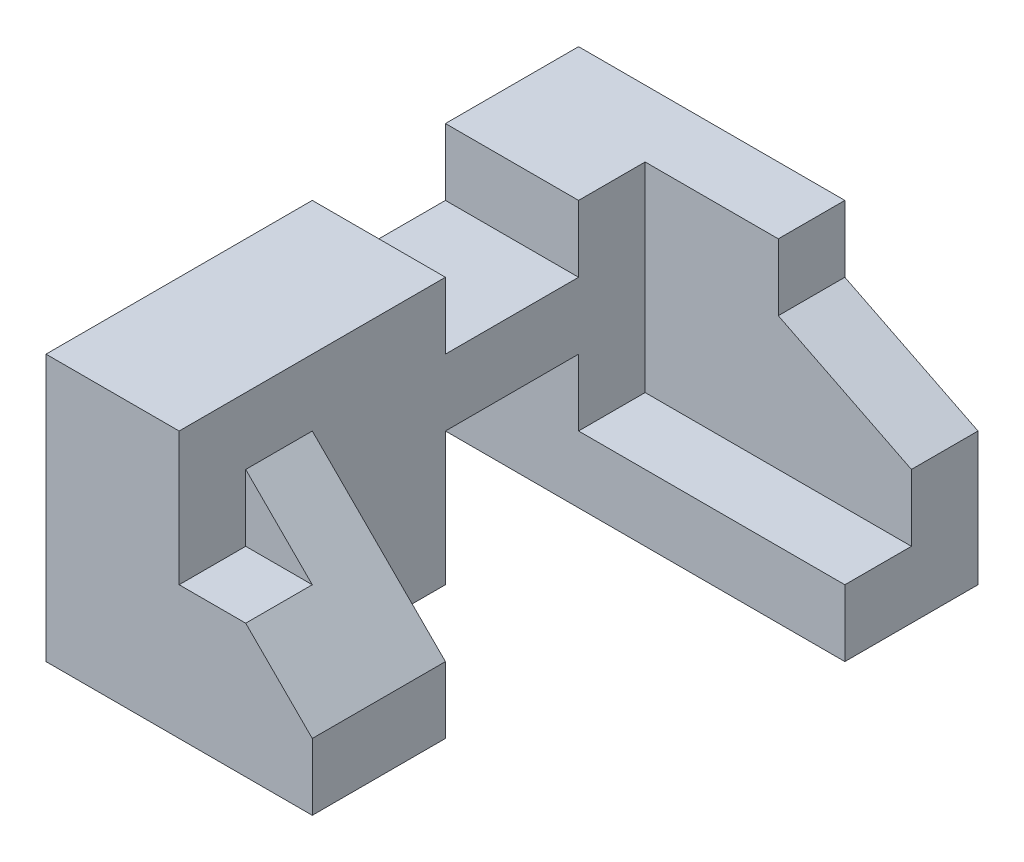
SolidWorks part; units mm, degrees
ref_plane "Front Plane" through (0, 0, 0) normal (0, 0, 1) x (1, 0, 0)
ref_plane "Top Plane" through (0, 0, 0) normal (0, 1, 0) x (1, 0, 0)
ref_plane "Right Plane" through (0, 0, 0) normal (1, 0, 0) x (0, 0, -1)
sketch "Sketch1" plane through (0, 0, 0) normal (0, 0, 1) x (1, 0, 0)
  line L1 (3, -2) -> (-3, -2)
  line L2 (3, -2) -> (3, 2)
  line L3 (3, 2) -> (-3, 2)
  line L4 (-3, -2) -> (-3, 2)
  line L5 (3, -2) -> (-3, 2) construction
  line L6 (3, 2) -> (-3, -2) construction
  point P0 (0, 0)
  dimension "D1" = 6
  dimension "D2" = 4
extrude "Boss-Extrude1" add sketch "Sketch1" along normal blind 8
sketch "Sketch2" plane through (0, 2, 0) normal (0, 1, 0) x (1, 0, 0)
  line L0 (-3, -2) -> (-1, -2)
  line L1 (-3, -8) -> (-3, 0) construction
  line L2 (-1, -2) -> (-1, -4)
  line L3 (-1, -4) -> (-3, -4)
  line L4 (-3, -4) -> (-3, -2)
  dimension "D1" = 2
  dimension "D2" = 2
  dimension "D3" = 2
extrude "Cut-Extrude1" cut sketch "Sketch2" against normal blind 1
sketch "Sketch4" plane through (3, 0, 0) normal (1, 0, 0) x (0, 0, -1)
  line L0 (-1, 2) -> (-1, -1)
  line L1 (-8, 2) -> (0, 2) construction
  line L2 (-8, -2) -> (0, -2) construction
  line L3 (-1, -1) -> (-6, -1)
  line L4 (-6, -1) -> (-6, 2)
  line L5 (-6, 2) -> (-1, 2)
  dimension "D1" = 1
  dimension "D2" = 5
  dimension "D3" = 1
extrude "Cut-Extrude13" cut sketch "Sketch4" against normal blind 4
sketch "Sketch5" plane through (3, 0, 0) normal (1, 0, 0) x (0, 0, -1)
  line L0 (-2, -1) -> (-2, -2)
  line L1 (-6, -1) -> (-1, -1) construction
  line L2 (-8, -2) -> (0, -2) construction
  line L3 (-2, -2) -> (-6, -2)
  line L4 (-6, -2) -> (-6, -1)
  line L5 (-6, -1) -> (-2, -1)
  dimension "D1" = 1
extrude "Cut-Extrude14" cut sketch "Sketch5" against normal blind 4
sketch "Sketch6" plane through (-1, 0, 0) normal (1, 0, 0) x (0, 0, -1)
  line L0 (-2, -2) -> (-2, 0)
  line L1 (-2, 0) -> (-4, 0)
  line L2 (-4, 0) -> (-4, -2)
  line L3 (-6, -2) -> (-2, -2) construction
  line L4 (-4, -2) -> (-2, -2)
  dimension "D1" = 2
extrude "Cut-Extrude15" cut sketch "Sketch6" against normal through all
sketch "Sketch7" plane through (0, 0, 0) normal (0, 0, -1) x (-1, 0, 0)
  line L0 (-1, 2) -> (-1, 1)
  line L1 (-3, 2) -> (3, 2) construction
  line L2 (-1, 1) -> (-3, 0)
  line L3 (-3, -2) -> (-3, 2) construction
  line L4 (-3, 0) -> (-3, 2)
  line L5 (-3, 2) -> (-1, 2)
  dimension "D1" = 1
  dimension "D2" = 2
  dimension "D3" = 2
extrude "Cut-Extrude16" cut sketch "Sketch7" against normal blind 1
sketch "Sketch8" plane through (0, 2, 0) normal (0, 1, 0) x (1, 0, 0)
  line L0 (-1, -8) -> (-1, -7)
  line L1 (3, -8) -> (-3, -8) construction
  line L2 (-1, -7) -> (0, -7)
  line L3 (0, -7) -> (0, -8)
  line L4 (0, -8) -> (-1, -8)
  dimension "D1" = 2
  dimension "D2" = 1
extrude "Cut-Extrude17" cut sketch "Sketch8" against normal blind 2
sketch "Sketch10" plane through (0, 2, 0) normal (0, 1, 0) x (1, 0, 0)
  line L0 (3, -6) -> (1, -6)
  line L1 (-1, -6) -> (3, -6) construction
  line L2 (1, -6) -> (1, -8)
  line L3 (3, -8) -> (0, -8) construction
  line L4 (1, -8) -> (3, -8)
  line L5 (3, -8) -> (3, -6)
  dimension "D1" = 4
extrude "Cut-Extrude18" cut sketch "Sketch10" against normal through all
sketch "Sketch12" plane through (1, 0, 0) normal (1, 0, 0) x (0, 0, -1)
  line L0 (-6, 2) -> (-6, 1)
  line L1 (-6, -2) -> (-6, 2) construction
  line L2 (-6, 1) -> (-8, 1)
  line L3 (-8, -2) -> (-8, 2) construction
  line L4 (-8, 1) -> (-8, 2)
  line L5 (-8, 2) -> (-6, 2)
  dimension "D1" = 1
extrude "Cut-Extrude19" cut sketch "Sketch12" against normal blind 2
sketch "Sketch13" plane through (0, 0, 8) normal (0, 0, 1) x (1, 0, 0)
  line L0 (1, -1) -> (-1, 1)
  line L1 (-1, -1) -> (3, -1) construction
  line L2 (-1, 0) -> (-1, 2) construction
  line L3 (-1, 1) -> (1, 1)
  line L4 (1, 1) -> (1, -1)
extrude "Cut-Extrude20" cut sketch "Sketch13" against normal blind 2
